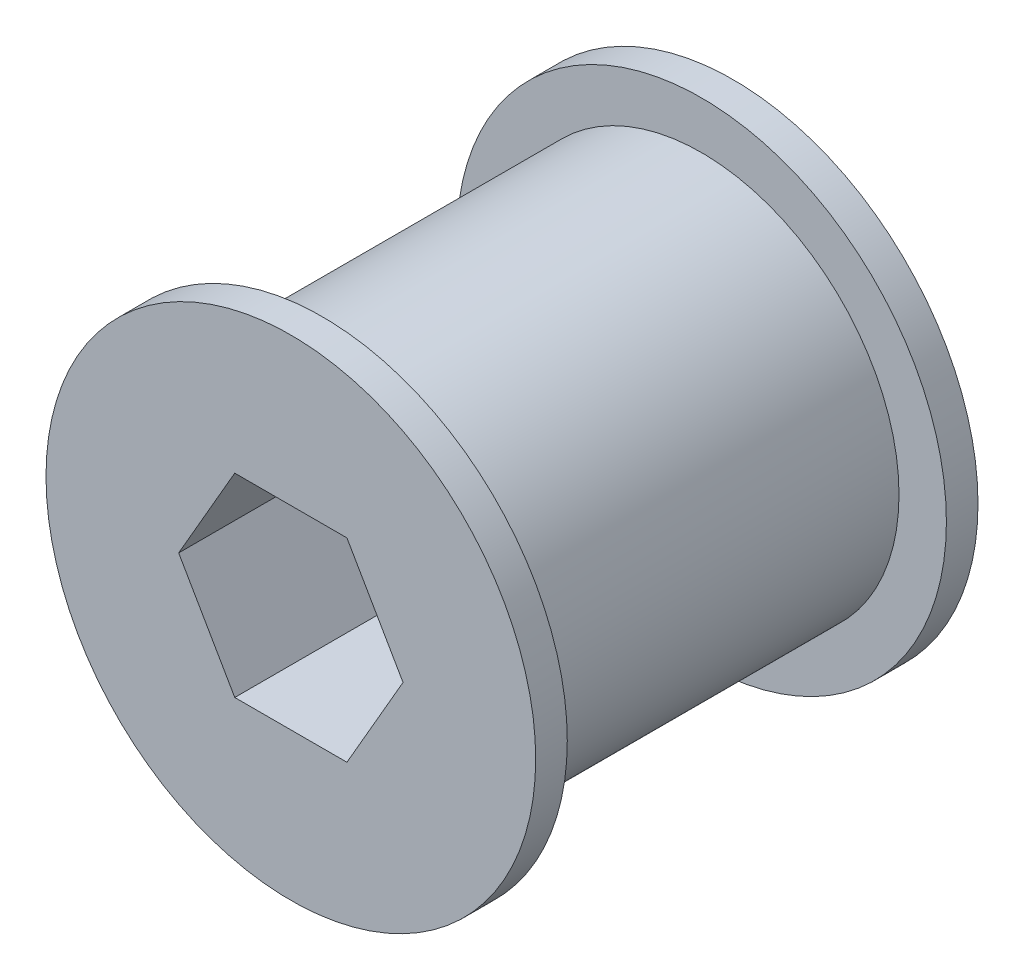
SolidWorks part; units mm, degrees
ref_plane "Front Plane" through (0, 0, 0) normal (0, 0, 1) x (1, 0, 0)
ref_plane "Top Plane" through (0, 0, 0) normal (0, 1, 0) x (1, 0, 0)
ref_plane "Right Plane" through (0, 0, 0) normal (1, 0, 0) x (0, 0, -1)
other "Configuration Table"
sketch "Sketch1" plane through (0, 0, 0) normal (0, 0, 1) x (1, 0, 0)
  circle A0 centre (0, 0) radius 12.5
  dimension "D2" = 25
extrude "Boss-Extrude1" add sketch "Sketch1" along normal blind 12
sketch "Sketch2" plane through (0, 0, 12) normal (0, 0, -1) x (-1, 0, 0)
  circle A3 centre (0, 0) radius 15.5
  circle A4 centre (0, 0) radius 15.5
  dimension "D1" = 3
extrude "Boss-Extrude2" add sketch "Sketch2" against normal blind 2
sketch "Sketch3" plane through (0, 0, 0) normal (0, 0, 1) x (1, 0, 0)
  line L1 (3.5507, -6.15) -> (7.1014, 0)
  line L2 (7.1014, 0) -> (3.5507, 6.15)
  line L3 (3.5507, 6.15) -> (-3.5507, 6.15)
  line L4 (-3.5507, 6.15) -> (-7.1014, 0)
  line L5 (-7.1014, 0) -> (-3.5507, -6.15)
  line L6 (-3.5507, -6.15) -> (3.5507, -6.15)
  circle A0 centre (0, 0) radius 6.15 construction
  dimension "D1" = 12.3
extrude "Cut-Extrude1" cut sketch "Sketch3" against normal up to surface (14 mm away)
mirror "Mirror1" about plane through (0, 0, 0) normal (0, 0, 1) of "Boss-Extrude2", "Boss-Extrude1"
sketch "Sketch5" plane through (0, 0, 0) normal (0, 0, 1) x (1, 0, 0)
  circle A0 centre (0, 0) radius 2.2
  dimension "D1" = 4.4
extrude "Cut-Extrude2" cut sketch "Sketch5" against normal up to surface (14 mm away) up to face at (-15.5, 0, -14)
sketch "Sketch6" plane through (0, 0, -14) normal (0, 0, -1) x (-1, 0, 0)
  circle A0 centre (0, 0) radius 6.15
  dimension "D1" = 12.3
extrude "Cut-Extrude3" cut sketch "Sketch6" against normal offset from surface (10 mm away) 4 up to face at (2.2, 0, 0)
